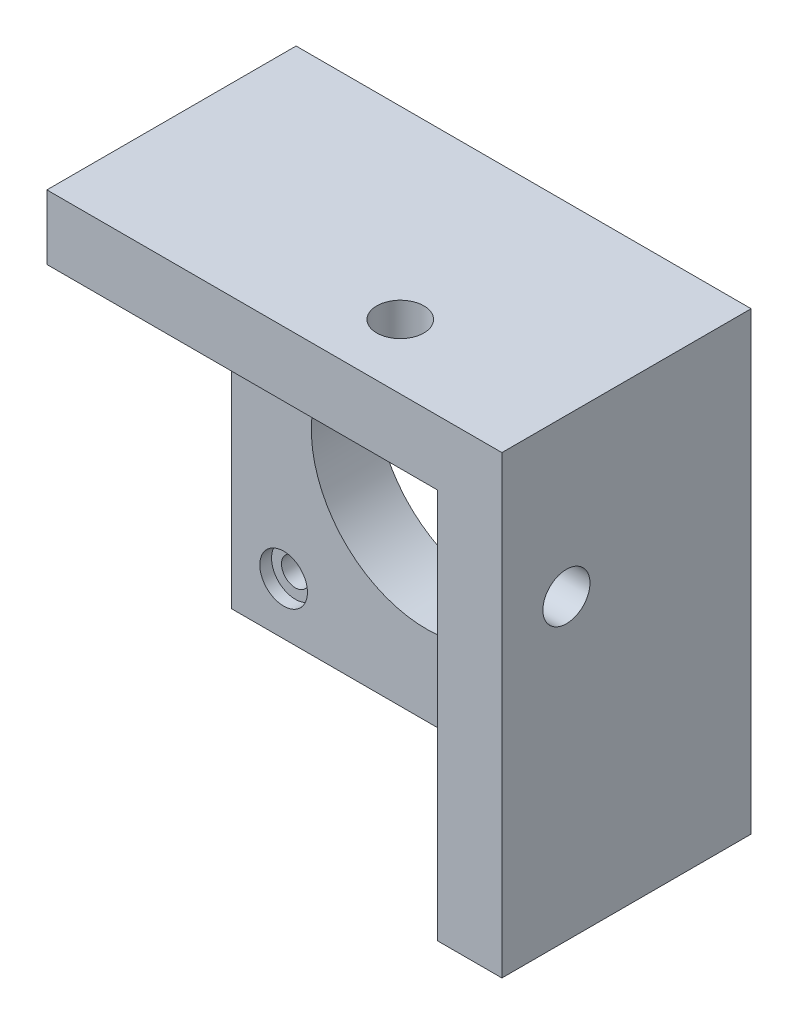
SolidWorks part; units mm, degrees
ref_plane "Front Plane" through (0, 0, 0) normal (0, 0, 1) x (1, 0, 0)
ref_plane "Top Plane" through (0, 0, 0) normal (0, 1, 0) x (1, 0, 0)
ref_plane "Right Plane" through (0, 0, 0) normal (1, 0, 0) x (0, 0, -1)
sketch "Sketch1" plane through (0, 0, 0) normal (0, 0, 1) x (1, 0, 0)
  line L1 (-21.15, -21.15) -> (21.15, -21.15)
  line L2 (-21.15, -21.15) -> (-21.15, 21.15)
  line L3 (-21.15, 21.15) -> (21.15, 21.15)
  line L4 (21.15, -21.15) -> (21.15, 21.15)
  line L5 (-21.15, -21.15) -> (21.15, 21.15) construction
  line L6 (-21.15, 21.15) -> (21.15, -21.15) construction
  point P0 (0, 0)
  point P6 (0, 0)
  point P7 (-33.1814, 30.5852)
  dimension "D1" = 42.3
  dimension "D2" = 42.3
extrude "Boss-Extrude1" add sketch "Sketch1" along normal blind 7
sketch "Sketch2" plane through (0, 0, 7) normal (0, 0, 1) x (1, 0, 0)
  line L2 (-21.15, 21.15) -> (-21.15, -21.15) construction
  line L3 (21.15, 21.15) -> (-21.15, 21.15) construction
  line L4 (-21.15, -21.15) -> (21.15, -21.15) construction
  circle A0 centre (-15.5, 15.5) radius 1.5
  circle A1 centre (0, 0) radius 12.5
  circle A5 centre (15.5, 15.5) radius 1.5
  circle A6 centre (15.5, -15.5) radius 1.5
  circle A7 centre (-15.5, -15.5) radius 1.5
  dimension "D1" = 3
  dimension "D7" = 25
  dimension "D3" = 5.65
  dimension "D4" = 5.65
  dimension "D6" = 5.65
  dimension "D2" = 2
  dimension "D5" = 2
extrude "Cut-Extrude1" cut sketch "Sketch2" against normal blind 7
sketch "Sketch3" plane through (0, 0, 7) normal (0, 0, 1) x (1, 0, 0)
  line L2 (21.15, 21.15) -> (21.15, -21.15)
  line L3 (21.15, -21.15) -> (28.15, -21.15)
  line L4 (28.15, 21.15) -> (28.15, -21.15)
  line L6 (21.15, 21.15) -> (21.15, 28.15)
  line L7 (21.15, 28.15) -> (28.15, 28.15)
  line L8 (28.15, 21.15) -> (28.15, 28.15)
  dimension "D1" = 7
  dimension "D2" = 7
extrude "Boss-Extrude2" add sketch "Sketch3" along normal blind 20 and the other way blind 7 separate body
sketch "Sketch4" plane through (0, 0, 7) normal (0, 0, 1) x (1, 0, 0)
  circle A0 centre (-15.5, 15.5) radius 2.58
  circle A1 centre (15.5, 15.5) radius 2.58
  circle A2 centre (-15.5, -15.5) radius 2.58
  circle A3 centre (15.5, -15.5) radius 2.58
extrude "Cut-Extrude2" cut sketch "Sketch4" against normal blind 1.27
sketch "Sketch5" plane through (0, 0, 7) normal (0, 0, 1) x (1, 0, 0)
  line L0 (21.15, 21.15) -> (21.15, 28.15)
  line L1 (21.15, 21.15) -> (-21.15, 21.15)
  line L2 (-21.15, 21.15) -> (-21.15, 28.15)
  line L3 (-21.15, 28.15) -> (21.15, 28.15)
extrude "Boss-Extrude3" add sketch "Sketch5" along normal blind 20 and the other way blind 7
sketch "Sketch6" plane through (0, 21.15, 0) normal (0, -1, 0) x (1, 0, 0)
  line L0 (-21.15, 7) -> (21.15, 7) construction
  line L3 (21.15, 0) -> (21.15, 27) construction
  circle A0 centre (10.15, 20.01) radius 2.5527
  dimension "D1" = 5.1054
  dimension "D2" = 11
  dimension "D3" = 13.01
extrude "Cut-Extrude3" cut sketch "Sketch6" against normal through all
sketch "Sketch7" plane through (21.15, 0, 0) normal (-1, 0, 0) x (0, 0, 1)
  line L0 (0, 21.15) -> (27, 21.15) construction
  line L1 (7, 21.15) -> (7, -21.15) construction
  circle A0 centre (20.01, 11.15) radius 2.5527
  dimension "D3" = 5.1054
  dimension "D1" = 10
  dimension "D2" = 13.01
extrude "Cut-Extrude4" cut sketch "Sketch7" against normal through all
